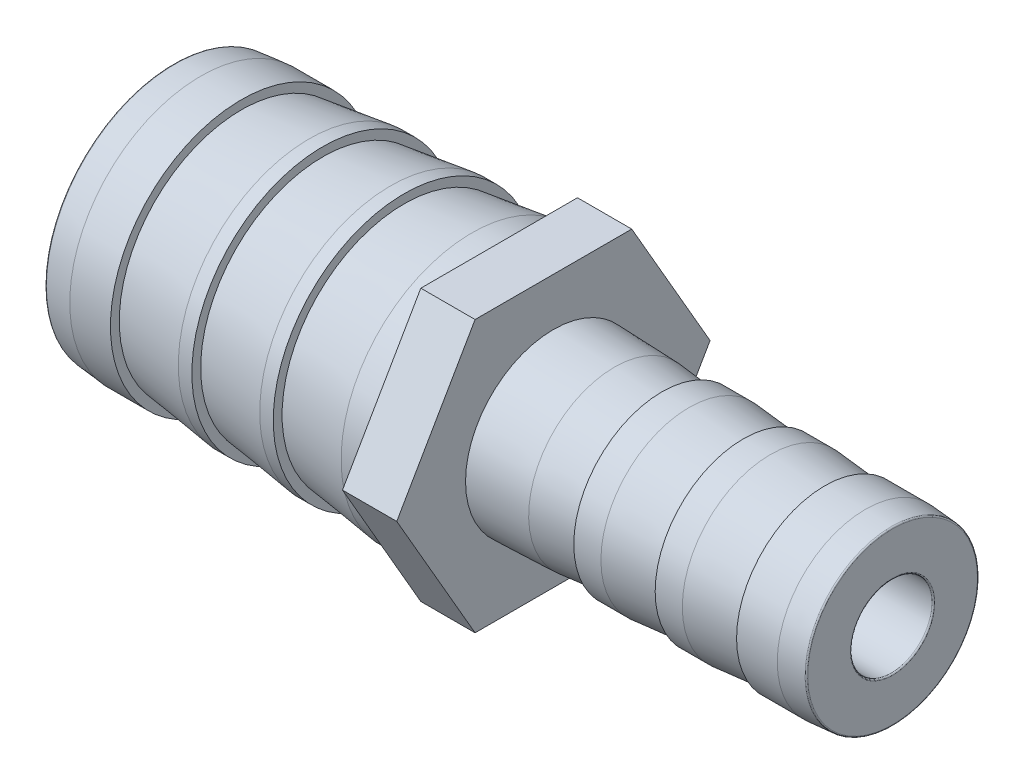
SolidWorks part; units mm, degrees
ref_plane "Front Plane" through (0, 0, 0) normal (0, 0, 1) x (1, 0, 0)
ref_plane "Top Plane" through (0, 0, 0) normal (0, 1, 0) x (1, 0, 0)
ref_plane "Right Plane" through (0, 0, 0) normal (1, 0, 0) x (0, 0, -1)
ref_plane "Plane1" through (2, 0, 0) normal (1, 0, 0) x (0, 0, -1)
sketch "Sketch1" plane through (2, 0, 0) normal (1, 0, 0) x (0, 0, -1)
  line L0 (11.547, 0) -> (5.7735, 10)
  line L1 (5.7735, 10) -> (-5.7735, 10)
  line L2 (-5.7735, 10) -> (-11.547, 0)
  line L3 (-11.547, 0) -> (-5.7735, -10)
  line L4 (-5.7735, -10) -> (5.7735, -10)
  line L5 (5.7735, -10) -> (11.547, 0)
extrude "Boss-Extrude1" add sketch "Sketch1" against normal blind 4
sketch "Sketch2" plane through (0, 0, 0) normal (0, 0, 1) x (1, 0, 0)
  line L0 (-26, 9.45) -> (-26, 0)
  line L1 (-26, 0) -> (-2, 0)
  line L2 (-2, 0) -> (-2, 9.65)
  line L3 (-2, 9.65) -> (-4, 9.65)
  line L4 (-4, 9.65) -> (-9, 9)
  line L5 (-9, 9) -> (-9, 9.65)
  line L6 (-9, 9.65) -> (-10, 9.65)
  line L7 (-10, 9.65) -> (-15, 9)
  line L8 (-15, 9) -> (-15, 9.65)
  line L9 (-15, 9.65) -> (-16, 9.65)
  line L10 (-16, 9.65) -> (-21, 9)
  line L11 (-21, 9) -> (-21, 9.65)
  line L12 (-21, 9.65) -> (-24, 9.65)
  line L13 (-24, 9.65) -> (-26, 9.45)
  line L14 (-26, 0) -> (-2, 0) construction
revolve "Revolve1" add sketch "Sketch2" angle 360 about L14
sketch "Sketch3" plane through (0, 0, 0) normal (0, 0, 1) x (1, 0, 0)
  line L0 (2, 6.477) -> (2, 0)
  line L1 (2, 0) -> (27, 0)
  line L2 (27, 0) -> (27, 6.35)
  line L3 (27, 6.35) -> (25, 6.5)
  line L4 (25, 6.5) -> (22, 6.5)
  line L5 (22, 6.5) -> (22, 6.15)
  line L6 (22, 6.15) -> (18, 6.5)
  line L7 (18, 6.5) -> (16, 6.5)
  line L8 (16, 6.5) -> (16, 6.15)
  line L9 (16, 6.15) -> (12, 6.5)
  line L10 (12, 6.5) -> (10, 6.5)
  line L11 (10, 6.5) -> (10, 5.977)
  line L12 (10, 5.977) -> (6.5, 6.327)
  line L13 (6.5, 6.327) -> (2, 6.477)
  line L14 (2, 0) -> (27, 0) construction
revolve "Revolve2" add sketch "Sketch3" angle 360 about L14
hole_wizard "Hole1" positions "Sketch5" profile "Sketch4" legacy
sketch "Sketch5" plane through (-26, 0, 0) normal (-1, 0, 0) x (0, 0, 1)
  point P0 (0, 0)
sketch "Sketch4" plane through (-26, 0, 0) normal (0, 1, 0) x (0, 0, 1)
  line L0 (0, 0) -> (0, 53)
  line L1 (0, 53) -> (3, 53)
  line L2 (3, 53) -> (3, 24)
  line L3 (3, 24) -> (8.4, 24)
  line L4 (8.4, 24) -> (8.4, 0)
  line L5 (8.4, 0) -> (0, 0)
  line L6 (0, 110) -> (0, -10) construction
  dimension "Diameter" = 6
  dimension "Depth" = 53
  dimension "C-Bore Diameter" = 16.8
  dimension "C-Bore Depth" = 24
fillet "Fillet1" radius 0.1 4 edges at (-26, 0, 8.4) (27, 0, 3) (27, 6.35, 0) (-26, 0, -9.45)
scale "Scale1" scale about centroid uniform scaling yes scale factor 0.92
